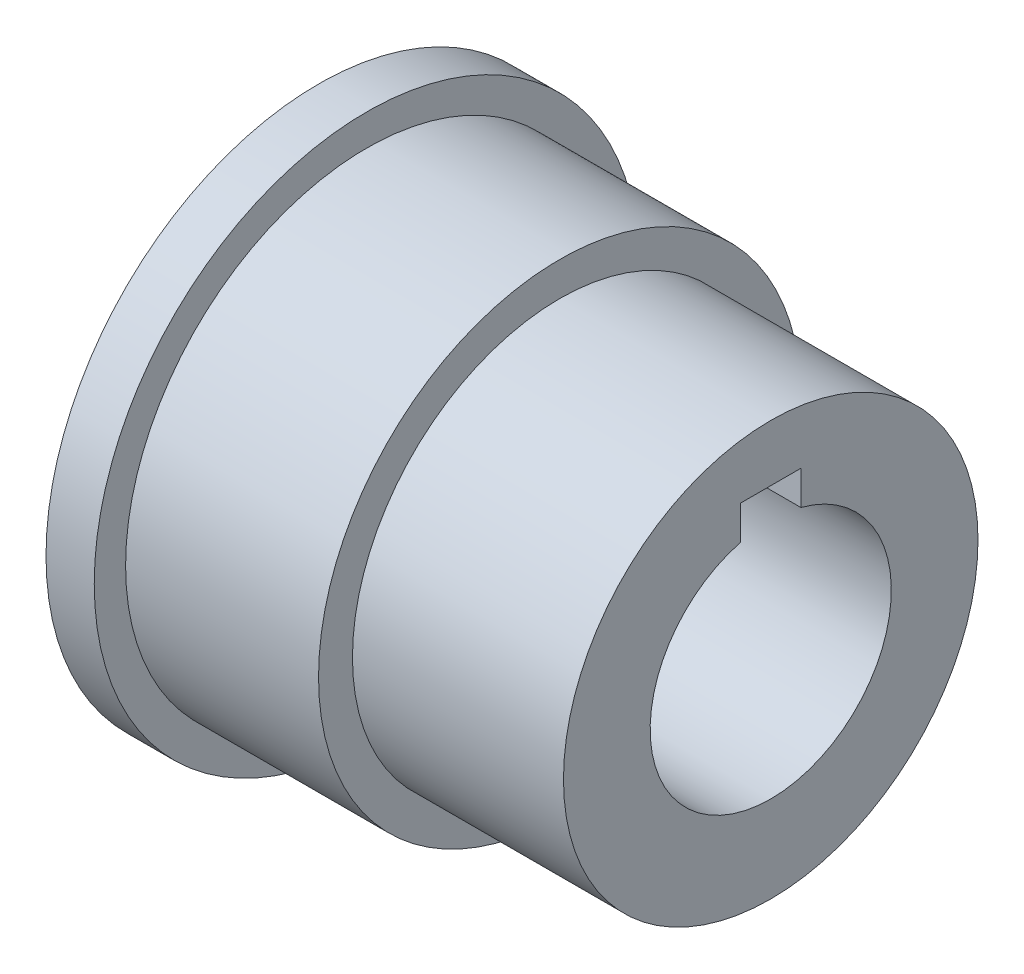
SolidWorks part; units mm, degrees
material "Plain Carbon Steel"
ref_plane "Front Plane" through (0, 0, 0) normal (0, 0, 1) x (1, 0, 0)
ref_plane "Top Plane" through (0, 0, 0) normal (0, 1, 0) x (1, 0, 0)
ref_plane "Right Plane" through (0, 0, 0) normal (1, 0, 0) x (0, 0, -1)
sketch "Sketch1" plane through (0, 0, 0) normal (1, 0, 0) x (0, 0, -1)
  line L0 (0, 7.9375) -> (0, 4.7625) construction
  line L1 (-1.5875, 7.9375) -> (1.5875, 7.9375)
  line L2 (-1.5875, 7.9375) -> (-1.5875, 4.7625)
  line L3 (-1.5875, 4.7625) -> (1.5875, 4.7625)
  line L4 (1.5875, 7.9375) -> (1.5875, 4.7625)
  line L5 (0, 4.7625) -> (1.5875, 6.35) construction
  line L6 (1.5875, 6.35) -> (-1.5875, 6.35) construction
  line L7 (0, 4.7625) -> (0, 0) construction
  circle A0 centre (0, 0) radius 6.35
  circle A1 centre (0, 0) radius 10.9141
  dimension "D1" = 6.35
  dimension "D2" = 1.5875
  dimension "D3" = 3.175
extrude "Boss-Extrude1" add sketch "Sketch1" along normal blind 23.8125 contours A1 A0 L2 L1 L4
sketch "Sketch2" plane through (0, 0, 0) normal (-1, 0, 0) x (0, 0, 1)
  circle A0 centre (0, 0) radius 10.9141
  circle A1 centre (0, 0) radius 12.7
extrude "Boss-Extrude2" add sketch "Sketch2" against normal blind 12.7
sketch "Sketch5" plane through (0, 0, 0) normal (-1, 0, 0) x (0, 0, 1)
  circle A0 centre (0, 0) radius 12.7
  circle A1 centre (0, 0) radius 14.351
extrude "Boss-Extrude3" add sketch "Sketch5" against normal blind 2.54
